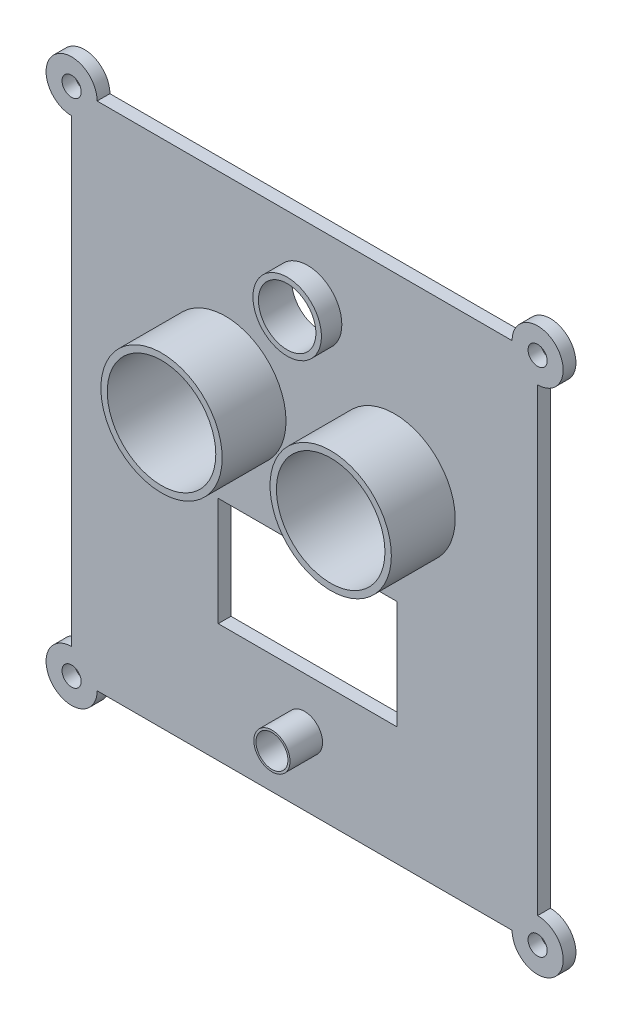
SolidWorks part; units mm, degrees
ref_plane "Front Plane" through (0, 0, 0) normal (0, 0, 1) x (1, 0, 0)
ref_plane "Top Plane" through (0, 0, 0) normal (0, 1, 0) x (1, 0, 0)
ref_plane "Right Plane" through (0, 0, 0) normal (1, 0, 0) x (0, 0, -1)
sketch "Sketch1" plane through (0, 0, 0) normal (0, 0, 1) x (1, 0, 0)
  line L0 (-13.5319, -11.4118) -> (14.4681, -11.4118)
  line L1 (-36.5, 50) -> (36.5, 50)
  line L2 (-36.5, 50) -> (-36.5, -30)
  line L3 (-36.5, -30) -> (36.5, -30)
  line L4 (36.5, 50) -> (36.5, -30)
  line L5 (-13.5319, -11.4118) -> (-13.5319, 5.5882)
  line L6 (-13.5319, 5.5882) -> (14.4681, 5.5882)
  line L36 (14.4681, -11.4118) -> (14.4681, 5.5882)
  line L37 (-13.5319, 5.5882) -> (14.4681, -11.4118) construction
  circle A17 centre (-12.4149, 21.373) radius 8.5
  circle A18 centre (14.0851, 21.373) radius 8.5
  circle A19 centre (0.4681, 38.8342) radius 4.5
  circle A20 centre (-0.0201, -19.3748) radius 2.5
  point P0 (0, 0)
  point P6 (0, 0)
  point P7 (0, 0)
  dimension "D3" = 17
  dimension "D4" = 17
  dimension "D1" = 80
  dimension "D2" = 73
extrude "Boss-Extrude3" add sketch "Sketch1" along normal blind 2
sketch "Sketch2" plane through (0, 0, 2) normal (0, 0, 1) x (1, 0, 0)
  circle A0 centre (-36.5, 50) radius 4
  circle A1 centre (36.5, 50) radius 4
  circle A2 centre (36.5, -30) radius 4
  circle A3 centre (-36.5, -30) radius 4
  dimension "D1" = 8
  dimension "D2" = 8
  dimension "D3" = 8
  dimension "D4" = 8
extrude "Boss-Extrude4" add sketch "Sketch2" against normal up to surface (2 mm away) up to face at (4.9681, 38.8342, 0)
sketch "Sketch3" plane through (0, 0, 2) normal (0, 0, 1) x (1, 0, 0)
  circle A0 centre (-36.5, 50) radius 1.5
  circle A1 centre (36.5, 50) radius 1.5
  circle A2 centre (36.5, -30) radius 1.5
  circle A3 centre (-36.5, -30) radius 1.5
  dimension "D1" = 3
  dimension "D2" = 3
  dimension "D3" = 3
  dimension "D4" = 3
extrude "Cut-Extrude1" cut sketch "Sketch3" against normal blind 10
sketch "Sketch4" plane through (0, 0, 2) normal (0, 0, 1) x (1, 0, 0)
  circle A0 centre (-12.4149, 21.373) radius 8.5
  circle A1 centre (-12.4149, 21.373) radius 9.5
  circle A2 centre (14.0851, 21.373) radius 8.5
  circle A3 centre (14.0851, 21.373) radius 9.5
  point P8 (0, 0)
  dimension "D1" = 17
  dimension "D2" = 17
  dimension "D3" = 19
  dimension "D4" = 19
extrude "Boss-Extrude5" add sketch "Sketch4" along normal blind 10
sketch "Sketch5" plane through (0, 0, 0) normal (0, 0, -1) x (-1, 0, 0)
  circle A0 centre (-0.4681, 38.8342) radius 4.5
  circle A1 centre (-0.4681, 38.8342) radius 5.3606
extrude "Boss-Extrude6" add sketch "Sketch5" against normal blind 5.2
sketch "Sketch7" plane through (0, 0, 2) normal (0, 0, 1) x (1, 0, 0)
  circle A0 centre (-0.0201, -19.3748) radius 2.5
  circle A1 centre (-0.0201, -19.3748) radius 2.834
extrude "Boss-Extrude7" add sketch "Sketch7" along normal blind 5.1
